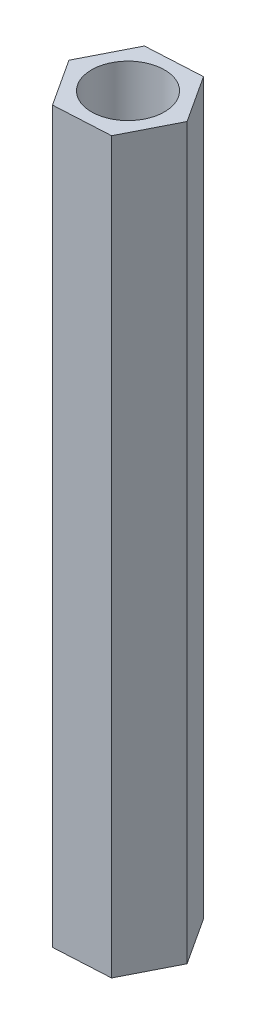
SolidWorks part; units mm, degrees
material "Brass"
ref_plane "Front Plane" through (0, 0, 0) normal (0, 0, 1) x (1, 0, 0)
ref_plane "Top Plane" through (0, 0, 0) normal (0, 1, 0) x (1, 0, 0)
ref_plane "Right Plane" through (0, 0, 0) normal (1, 0, 0) x (0, 0, -1)
sketch "Sketch1" plane through (0, 0, 0) normal (0, 1, 0) x (1, 0, 0)
  line L1 (-1.2602, 1.9353) -> (-2.3061, -0.1237)
  line L2 (-2.3061, -0.1237) -> (-1.0459, -2.059)
  line L3 (-1.0459, -2.059) -> (1.2602, -1.9353)
  line L4 (1.2602, -1.9353) -> (2.3061, 0.1237)
  line L5 (2.3061, 0.1237) -> (1.0459, 2.059)
  line L6 (1.0459, 2.059) -> (-1.2602, 1.9353)
  circle A0 centre (0, 0) radius 1.5
  circle A1 centre (0, 0) radius 2 construction
  dimension "D1" = 3
  dimension "D2" = 4
extrude "Boss-Extrude1" add sketch "Sketch1" along normal blind 30
